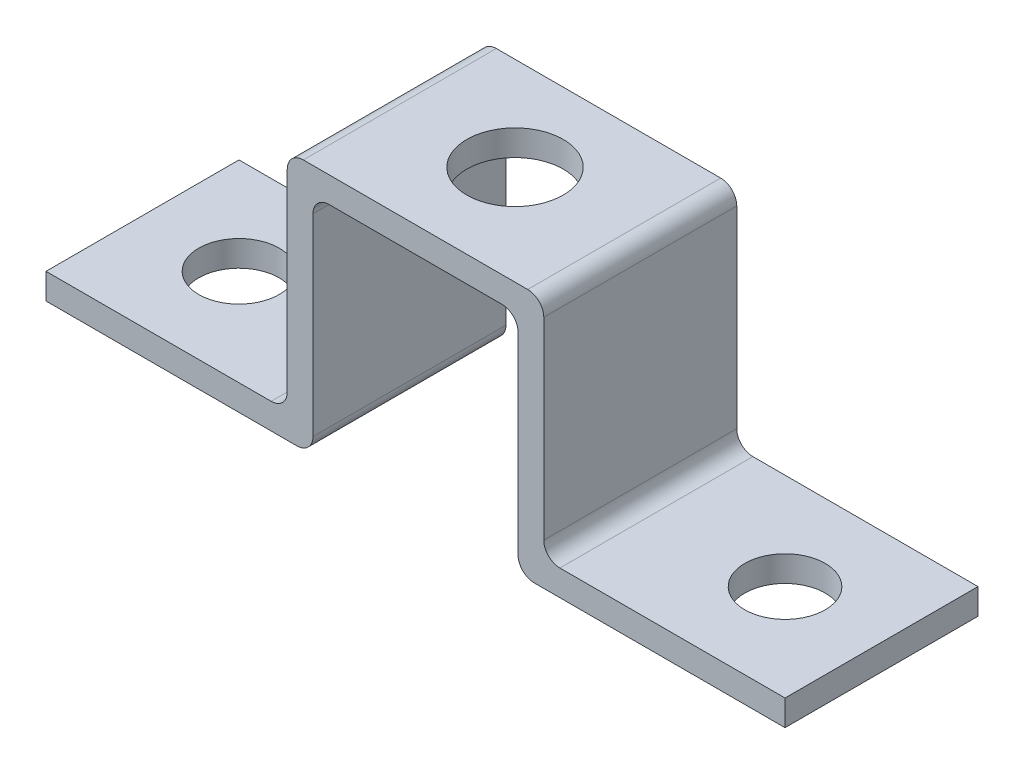
SolidWorks part; units mm, degrees
ref_plane "Front Plane" through (0, 0, 0) normal (0, 0, 1) x (1, 0, 0)
ref_plane "Top Plane" through (0, 0, 0) normal (0, 1, 0) x (1, 0, 0)
ref_plane "Right Plane" through (0, 0, 0) normal (1, 0, 0) x (0, 0, -1)
sketch "Sketch1" plane through (0, 0, 0) normal (0, 0, 1) x (1, 0, 0)
  line L0 (0, 77.3811) -> (0, -89.5992) construction
  line L1 (-22.9768, 1.2511) -> (-7.9768, 1.2511)
  line L2 (-7.9768, 1.2511) -> (-7.9768, 15.2511)
  line L3 (-7.9768, 15.2511) -> (7.9768, 15.2511)
  line L4 (-22.9768, 1.2511) -> (-22.9768, -0.3489)
  line L5 (-22.9768, -0.3489) -> (-6.3768, -0.3489)
  line L6 (-6.3768, -0.3489) -> (-6.3768, 13.6511)
  line L7 (-6.3768, 13.6511) -> (6.3768, 13.6511)
  line L8 (6.3768, -0.3489) -> (6.3768, 13.6511)
  line L9 (22.9768, -0.3489) -> (6.3768, -0.3489)
  line L10 (22.9768, 1.2511) -> (22.9768, -0.3489)
  line L11 (7.9768, 1.2511) -> (7.9768, 15.2511)
  line L12 (22.9768, 1.2511) -> (7.9768, 1.2511)
  point P12 (0, 13.6511)
  point P16 (0, 15.2511)
extrude "Boss-Extrude1" add sketch "Sketch1" along normal blind 12
sketch "Sketch2" plane through (0, 1.2511, 0) normal (0, 1, 0) x (1, 0, 0)
  circle A0 centre (-16.9768, -6) radius 2.5
  circle A1 centre (16.9768, -6) radius 2.5
extrude "Cut-Extrude2" cut sketch "Sketch2" against normal blind 1.6
sketch "Sketch3" plane through (0, 15.2511, 0) normal (0, 1, 0) x (1, 0, 0)
  circle A0 centre (0, -5.8126) radius 3
extrude "Cut-Extrude3" cut sketch "Sketch3" against normal blind 1.6
cosmetic thread "Cosmetic Thread2" parameters "D2"=7
fillet "Fillet2" radius 1 1 edges at (-7.9768, 15.2511, 6)
fillet "Fillet3" radius 1 1 edges at (7.9768, 15.2511, 6)
fillet "Fillet4" radius 1 1 edges at (-6.3768, 13.6511, 6)
fillet "Fillet5" radius 1 1 edges at (-6.3768, -0.3489, 6)
fillet "Fillet6" radius 1 1 edges at (6.3768, -0.3489, 6)
fillet "Fillet7" radius 1 1 edges at (6.3768, 13.6511, 6)
fillet "Fillet8" radius 1 1 edges at (-7.9768, 1.2511, 6)
fillet "Fillet9" radius 1 1 edges at (7.9768, 1.2511, 6)
